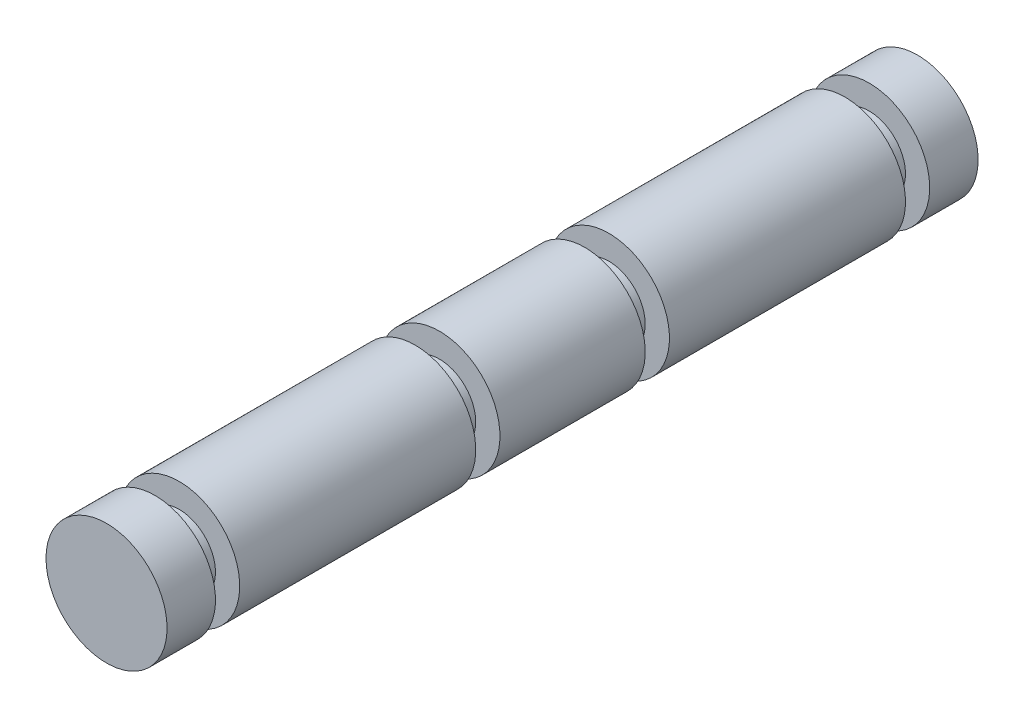
SolidWorks part; units mm, degrees
ref_plane "Front Plane" through (0, 0, 0) normal (0, 0, 1) x (1, 0, 0)
ref_plane "Top Plane" through (0, 0, 0) normal (0, 1, 0) x (1, 0, 0)
ref_plane "Right Plane" through (0, 0, 0) normal (1, 0, 0) x (0, 0, -1)
sketch "Sketch2" plane through (0, 0, 0) normal (0, 1, 0) x (1, 0, 0)
  line L1 (0, 67) -> (-5, 67)
  line L2 (0, 67) -> (0, 0)
  line L3 (0, 0) -> (-5, 0)
  line L4 (-5, 67) -> (-5, 0)
  line L5 (-5, 63) -> (-3, 63)
  line L6 (-5, 63) -> (-5, 61)
  line L7 (-5, 61) -> (-3, 61)
  line L8 (-3, 63) -> (-3, 61)
  line L9 (-5, 6) -> (-3, 6)
  line L10 (-5, 6) -> (-5, 4)
  line L11 (-5, 4) -> (-3, 4)
  line L12 (-3, 6) -> (-3, 4)
  line L13 (-5, 25.5) -> (-3, 25.5)
  line L14 (-5, 25.5) -> (-5, 27.5)
  line L15 (-5, 27.5) -> (-3, 27.5)
  line L16 (-3, 25.5) -> (-3, 27.5)
  line L17 (-5, 41.5) -> (-3, 41.5)
  line L18 (-5, 41.5) -> (-5, 39.5)
  line L19 (-5, 39.5) -> (-3, 39.5)
  line L20 (-3, 41.5) -> (-3, 39.5)
  point P20 (-4, 25.5)
  point P21 (-2.5, 67)
  point P22 (-3, 26.5)
  dimension "D1" = 67
  dimension "D2" = 2
  dimension "D3" = 2
  dimension "D4" = 2
  dimension "D5" = 2
  dimension "D6" = 4
  dimension "D7" = 4
  dimension "D8" = 5
  dimension "D9" = 2
  dimension "D10" = 2
  dimension "D11" = 25.5
  dimension "D12" = 25.5
  dimension "D13" = 2
  dimension "D14" = 2
  dimension "D15" = 67
  dimension "D16" = 0
  dimension "D17" = 0
revolve "Revolve1" add sketch "Sketch2" angle 360 about L2
